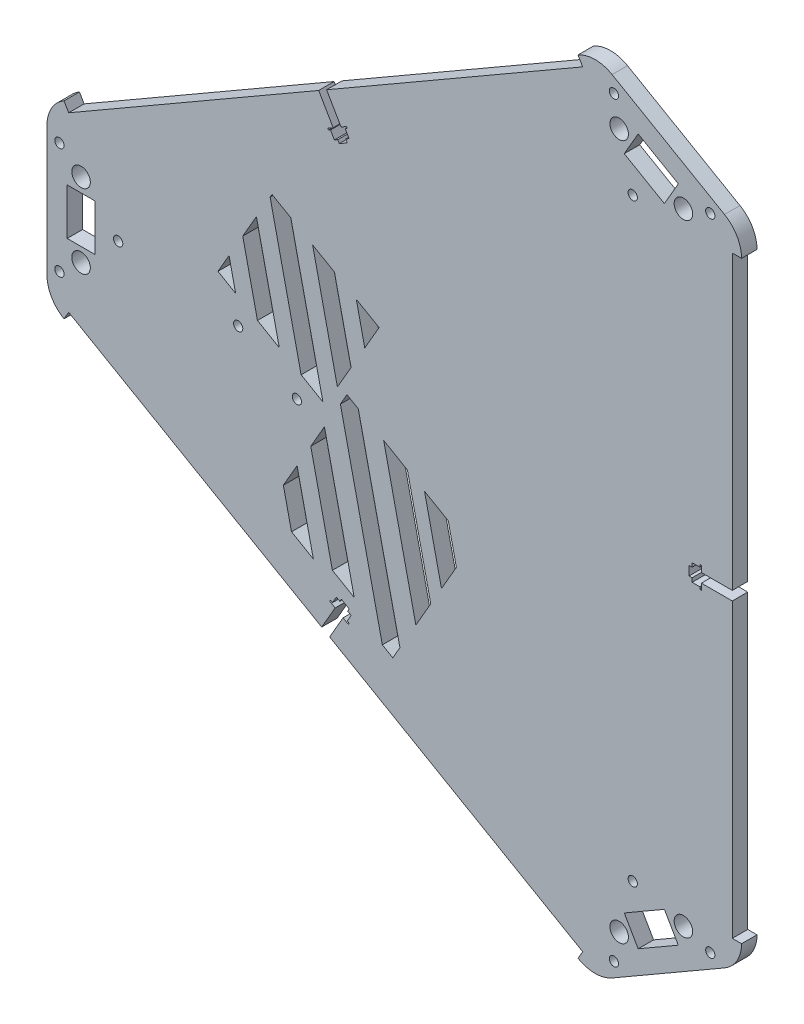
SolidWorks part; units mm, degrees
material "6061-T6 Black anodised"
ref_plane "Front Plane" through (0, 0, 0) normal (0, 0, 1) x (1, 0, 0)
ref_plane "Top Plane" through (0, 0, 0) normal (0, 1, 0) x (1, 0, 0)
ref_plane "Right Plane" through (0, 0, 0) normal (1, 0, 0) x (0, 0, -1)
sketch "Sketch1" plane through (0, 0, 0) normal (0, 0, 1) x (1, 0, 0)
  line L0 (0, 0) -> (-123, 0) construction
  line L1 (-123, 21) -> (-123, -21) construction
  line L2 (-131.025, 20.9813) -> (-131.025, -21) construction
  line L3 (0, 0) -> (61.5, 106.5211) construction
  line L4 (0, 0) -> (61.5, -106.5211) construction
  line L5 (43.3135, 117.0211) -> (79.6865, 96.0211) construction
  line L6 (79.6865, -96.0211) -> (43.3135, -117.0211) construction
  line L7 (47.326, 123.971) -> (83.699, 102.971) construction
  line L8 (83.699, -102.971) -> (47.326, -123.971) construction
  line L9 (-127.0125, 27.9499) -> (39.301, 123.971)
  line L10 (87.7115, 96.0211) -> (87.7115, -96.0211)
  line L11 (39.301, -123.971) -> (-127.0125, -27.9498)
  line L12 (57.2548, -114.1682) -> (70.2452, -106.6682)
  line L13 (57.2548, -114.1682) -> (52.7548, -106.374)
  line L14 (70.2452, -106.6682) -> (65.7452, -98.874)
  line L15 (52.7548, -106.374) -> (65.7452, -98.874)
  line L16 (57.2548, -114.1682) -> (65.7452, -98.874) construction
  line L17 (70.2452, -106.6682) -> (52.7548, -106.374) construction
  line L18 (-118.5, 7.5) -> (-118.5, -7.5)
  line L19 (-127.5, -7.5) -> (-118.5, -7.5)
  line L20 (-127.5, 7.5) -> (-127.5, -7.5)
  line L21 (-127.5, 7.5) -> (-118.5, 7.5)
  line L22 (65.7452, 98.874) -> (52.7548, 106.374)
  line L23 (57.2548, 114.1682) -> (52.7548, 106.374)
  line L24 (70.2452, 106.6682) -> (57.2548, 114.1682)
  line L25 (70.2452, 106.6682) -> (65.7452, 98.874)
  line L26 (-123, 21) -> (-99, 34.8564) construction
  line L27 (-99, 34.8564) -> (-99, -34.8564) construction
  line L28 (-99, -34.8564) -> (-123, -21) construction
  line L29 (-134.025, 21) -> (-134.025, -21)
  line L30 (-127.0125, 27.9499) -> (-128.5125, 30.5479)
  line L31 (-127.0125, -27.9498) -> (-128.5125, -30.5479)
  line L32 (39.301, 123.971) -> (37.801, 126.5691)
  line L33 (87.7115, 96.0211) -> (90.7115, 96.0211)
  line L34 (48.826, 126.5691) -> (85.199, 105.5691)
  line L35 (39.301, -123.971) -> (37.801, -126.5691)
  line L36 (87.7115, -96.0211) -> (90.7115, -96.0211)
  line L37 (48.826, -126.5691) -> (85.199, -105.5691)
  circle A0 centre (-123, 21) radius 4.025 construction
  circle A1 centre (-123, -21) radius 4.025 construction
  arc A2 (-127.0125, 27.9499) -> (-131.025, 20.9813) centre (-123, 21) ccw construction
  arc A3 (-131.025, -21) -> (-127.0125, -27.9498) centre (-123, -21) ccw construction
  circle A4 centre (43.3135, 117.0211) radius 4.025 construction
  circle A5 centre (79.6865, 96.0211) radius 4.025 construction
  circle A6 centre (79.6865, -96.0211) radius 4.025 construction
  circle A7 centre (43.3135, -117.0211) radius 4.025 construction
  arc A8 (39.301, -123.971) -> (47.326, -123.971) centre (43.3135, -117.0211) ccw construction
  arc A9 (83.699, -102.971) -> (87.7115, -96.0211) centre (79.6865, -96.0211) ccw construction
  arc A10 (87.7115, 96.0211) -> (83.699, 102.971) centre (79.6865, 96.0211) ccw construction
  arc A11 (47.326, 123.971) -> (39.301, 123.971) centre (43.3135, 117.0211) ccw construction
  circle A12 centre (-99, 34.8564) radius 1.65 construction
  circle A13 centre (-99, -34.8564) radius 1.65 construction
  circle A14 centre (79.6865, 68.3083) radius 1.65 construction
  circle A15 centre (19.3135, 103.1647) radius 1.65 construction
  circle A16 centre (19.3135, -103.1647) radius 1.65 construction
  circle A17 centre (79.6865, -68.3083) radius 1.65 construction
  circle A18 centre (0, 0) radius 65 construction
  arc A19 (-134.025, 21) -> (-128.5125, 30.5479) centre (-123, 21) cw
  arc A20 (-134.025, -21) -> (-128.5125, -30.5479) centre (-123, -21) ccw
  arc A21 (48.826, 126.5691) -> (37.801, 126.5691) centre (43.3135, 117.0211) ccw
  arc A22 (90.7115, 96.0211) -> (85.199, 105.5691) centre (79.6865, 96.0211) ccw
  arc A23 (37.801, -126.5691) -> (48.826, -126.5691) centre (43.3135, -117.0211) ccw
  arc A24 (85.199, -105.5691) -> (90.7115, -96.0211) centre (79.6865, -96.0211) ccw
  circle A25 centre (-123, 12) radius 3
  circle A26 centre (-123, -12) radius 3
  circle A27 centre (71.8923, 100.5211) radius 3
  circle A28 centre (51.1077, 112.5211) radius 3
  circle A29 centre (51.1077, -112.5211) radius 3
  circle A30 centre (71.8923, -100.5211) radius 3
  circle A31 centre (-111, 0) radius 1.5
  circle A32 centre (55.5, 96.1288) radius 1.5
  circle A33 centre (55.5, -96.1288) radius 1.5
  circle A34 centre (-130, 18) radius 1.5
  circle A35 centre (-130, -18) radius 1.5
  circle A36 centre (80.5885, 103.5833) radius 1.5
  circle A37 centre (49.4115, 121.5833) radius 1.5
  circle A38 centre (49.4115, -121.5833) radius 1.5
  circle A39 centre (80.5885, -103.5833) radius 1.5
  point P44 (0, 0)
  point P56 (0, 0)
  point P79 (0, 0)
  point P84 (0, 0)
  point P91 (0, 0)
  point P104 (0, 0)
  dimension "D3" = 8.05
  dimension "D9" = 3.3
  dimension "D12" = 130
  dimension "D15" = 6
  dimension "D18" = 3
  dimension "D24" = 3
  dimension "D1" = 123
  dimension "D2" = 42
  dimension "D4" = 120
  dimension "D5" = 4
  dimension "D6" = 9
  dimension "D7" = 15
  dimension "D10" = 24
  dimension "D13" = 3
  dimension "D14" = 12
  dimension "D16" = 12
  dimension "D19" = 12
  dimension "D21" = 3
  dimension "D22" = 7
  dimension "D8" = 3
  dimension "D11" = 3
  dimension "D17" = 3
  dimension "D20" = 3
  dimension "D23" = 3
extrude "Boss-Extrude1" add sketch "Sketch1" along normal blind 5
sketch "Sketch2" plane through (0, 0, 5) normal (0, 0, 1) x (1, 0, 0)
  line L0 (0, 0) -> (87.7115, 0) construction
  line L1 (87.7115, -96.0211) -> (87.7115, 96.0211) construction
  line L2 (87.7115, 1.48) -> (77.7115, 1.48)
  line L3 (77.7115, 1.48) -> (77.7115, 3.5)
  line L4 (77.7115, 3.5) -> (77.2115, 3.5)
  line L5 (77.2115, 3.5) -> (77.2115, 2.75)
  line L6 (77.2115, 2.75) -> (74.7115, 2.75)
  line L7 (74.7115, 2.75) -> (74.7115, 1.48)
  line L8 (74.7115, 1.48) -> (73.7115, 1.48)
  line L9 (73.7115, 1.48) -> (73.7115, -1.48)
  line L10 (87.7115, -1.48) -> (87.7115, 1.48)
  line L11 (74.7115, -1.48) -> (73.7115, -1.48)
  line L12 (74.7115, -2.75) -> (74.7115, -1.48)
  line L13 (77.2115, -2.75) -> (74.7115, -2.75)
  line L14 (77.2115, -3.5) -> (77.2115, -2.75)
  line L15 (77.7115, -3.5) -> (77.2115, -3.5)
  line L16 (77.7115, -1.48) -> (77.7115, -3.5)
  line L17 (87.7115, -1.48) -> (77.7115, -1.48)
  line L18 (-43.2236, -77.8254) -> (-38.2236, -69.1652)
  line L19 (-38.2236, -69.1652) -> (-36.4742, -70.1752)
  line L20 (-36.4742, -70.1752) -> (-36.2242, -69.7421)
  line L21 (-36.2242, -69.7421) -> (-36.8737, -69.3671)
  line L22 (-36.8737, -69.3671) -> (-35.6237, -67.2021)
  line L23 (-35.6237, -67.2021) -> (-36.7236, -66.5671)
  line L24 (-36.7236, -66.5671) -> (-36.2236, -65.7011)
  line L25 (-36.2236, -65.7011) -> (-38.787, -64.2211)
  line L26 (-39.287, -65.0871) -> (-38.787, -64.2211)
  line L27 (-40.3869, -64.4521) -> (-39.287, -65.0871)
  line L28 (-41.6369, -66.6171) -> (-40.3869, -64.4521)
  line L29 (-42.2864, -66.2421) -> (-41.6369, -66.6171)
  line L30 (-42.5364, -66.6752) -> (-42.2864, -66.2421)
  line L31 (-40.787, -67.6852) -> (-42.5364, -66.6752)
  line L32 (-45.787, -76.3454) -> (-40.787, -67.6852)
  line L33 (-45.787, -76.3454) -> (-43.2236, -77.8254)
  line L34 (-46.4365, 75.2204) -> (-41.4365, 66.5602)
  line L35 (-41.4365, 66.5602) -> (-43.1859, 65.5502)
  line L36 (-43.1859, 65.5502) -> (-42.9359, 65.1171)
  line L37 (-42.9359, 65.1171) -> (-42.2864, 65.4921)
  line L38 (-42.2864, 65.4921) -> (-41.0364, 63.3271)
  line L39 (-41.0364, 63.3271) -> (-39.9365, 63.9621)
  line L40 (-39.9365, 63.9621) -> (-39.4365, 63.0961)
  line L41 (-39.4365, 63.0961) -> (-36.8731, 64.5761)
  line L42 (-37.3731, 65.4421) -> (-36.8731, 64.5761)
  line L43 (-36.2732, 66.0771) -> (-37.3731, 65.4421)
  line L44 (-37.5232, 68.2421) -> (-36.2732, 66.0771)
  line L45 (-36.8737, 68.6171) -> (-37.5232, 68.2421)
  line L46 (-37.1237, 69.0502) -> (-36.8737, 68.6171)
  line L47 (-38.8731, 68.0402) -> (-37.1237, 69.0502)
  line L48 (-43.8731, 76.7004) -> (-38.8731, 68.0402)
  line L49 (-43.8731, 76.7004) -> (-46.4365, 75.2204)
  point P16 (73.7115, 0)
  point P56 (0.0125, 0.0072)
  point P58 (-0.6495, -0.375)
  point P59 (0, 0)
  dimension "D1" = 0.5
  dimension "D2" = 2.5
  dimension "D3" = 14
  dimension "D4" = 2.96
  dimension "D5" = 7
  dimension "D6" = 5.5
  dimension "D7" = 1
  dimension "D8" = 3
extrude "Cut-Extrude1" cut sketch "Sketch2" against normal through all
sketch "Sketch3" plane through (0, 0, 5) normal (0, 0, 1) x (1, 0, 0)
  line L0 (-36.9705, -6.0348) -> (-61.9705, -49.336) construction
  line L1 (-36.9705, -6.0348) -> (2.8667, -29.0348) construction
  line L2 (-61.9705, -49.336) -> (-22.1333, -72.3361) construction
  line L3 (2.8667, -29.0348) -> (-22.1333, -72.3361) construction
  line L4 (-36.9705, -6.0348) -> (-22.1333, -72.3361) construction
  line L5 (-61.9705, -49.336) -> (2.8667, -29.0348) construction
  line L6 (-36.8558, -63.8361) -> (-43.8558, -75.9604) construction
  line L7 (-42.574, -76.7004) -> (39.301, -123.971) construction
  line L8 (-57.5395, -41.6614) -> (-54.9098, -53.4125)
  line L9 (-54.9098, -53.4125) -> (-47.8492, -57.489)
  line L10 (-47.8492, -57.489) -> (-53.1086, -33.9868)
  line L11 (-53.1086, -33.9868) -> (-57.5395, -41.6614)
  line L12 (-48.6777, -26.3122) -> (-41.6788, -57.5874)
  line L13 (-35.5924, -64.5655) -> (-28.5317, -68.6419) construction
  line L14 (-34.6181, -61.6639) -> (-44.2467, -18.6376)
  line L15 (-44.2467, -18.6376) -> (-48.6777, -26.3122)
  line L16 (-39.0937, -9.7122) -> (-25.5166, -70.3827)
  line L17 (-25.5166, -70.3827) -> (-22.1333, -72.3361)
  line L18 (-22.1333, -72.3361) -> (-19.8255, -68.3389)
  line L19 (-19.8255, -68.3389) -> (-33.2931, -8.1579)
  line L20 (-44.2467, -18.6376) -> (-37.4373, -17.1137) construction
  line L21 (-25.0817, -12.8988) -> (-14.6725, -59.4135)
  line L22 (-14.6725, -59.4135) -> (-9.8562, -51.0715)
  line L23 (-9.8562, -51.0715) -> (-17.4071, -17.3297)
  line L24 (-17.4071, -17.3297) -> (-25.0817, -12.8988)
  line L25 (-11.8686, -20.5274) -> (-6.3805, -45.0514)
  line L26 (-6.3805, -45.0514) -> (-1.5643, -36.7094)
  line L27 (-1.5643, -36.7094) -> (-4.194, -24.9583)
  line L28 (-4.194, -24.9583) -> (-11.8686, -20.5274)
  line L29 (-33.2931, -8.1579) -> (-36.9705, -6.0348)
  line L30 (-36.9705, -6.0348) -> (-39.0937, -9.7122)
  line L31 (-25.0817, -12.8988) -> (-31.8911, -14.4226) construction
  line L32 (-45.1375, -75.2204) -> (-42.574, -76.7004) construction
  line L33 (-41.6788, -57.5874) -> (-34.6181, -61.6639)
  point P1 (-29.5519, -39.1854)
  dimension "D1" = 3
  dimension "D2" = 46
  dimension "D3" = 50
  dimension "D4" = 14
  dimension "D5" = 6
  dimension "D6" = 6
  dimension "D7" = 6
  dimension "D8" = 6
  dimension "D9" = 6
  dimension "D10" = 17
extrude "Cut-Extrude2" cut sketch "Sketch3" against normal through all
sketch "Sketch4" plane through (0, 0, 5) normal (0, 0, 1) x (1, 0, 0)
  line L0 (-127.0125, -27.9498) -> (-45.1375, -75.2204) construction
  line L1 (-128.5125, -30.5479) -> (-127.0125, -27.9498) construction
  circle A0 centre (-72.1758, -4.3808) radius 1.5
  circle A1 centre (-53.1624, -15.3581) radius 1.5
  dimension "D3" = 3
  dimension "D6" = 3
  dimension "D1" = 47.8298
  dimension "D2" = 35.7054
  dimension "D4" = 21.9547
  dimension "D5" = 47.8298
sketch "Sketch5" plane through (0, 0, 5) normal (0, 0, 1) x (1, 0, 0)
  line L0 (-71.5686, -59.9604) -> (-26.5686, 17.9819) construction
  line L1 (-127.0125, -27.9498) -> (-45.1375, -75.2204) construction
  line L2 (-26.5686, 17.9819) -> (-61.2096, 37.9819) construction
  line L3 (-61.2096, 37.9819) -> (-78.7096, 7.671) construction
  line L4 (-78.7096, 7.671) -> (-44.0686, -12.329) construction
  line L5 (-36.9705, -6.0348) -> (-39.0937, -9.7122) construction
  line L6 (-40.0613, -5.3882) -> (-48.069, 30.3952)
  line L7 (-48.069, 30.3952) -> (-41.0084, 26.3187)
  line L8 (-41.0084, 26.3187) -> (-35.6303, 2.2864)
  line L9 (-35.6303, 2.2864) -> (-40.0613, -5.3882)
  line L10 (-39.0937, -9.7122) -> (-25.5166, -70.3827) construction
  line L11 (-66.256, 29.2412) -> (-58.865, -3.7863)
  line L12 (-33.9477, 22.2422) -> (-31.1994, 9.961)
  line L13 (-31.1994, 9.961) -> (-26.5686, 17.9819)
  line L14 (-26.5686, 17.9819) -> (-33.9477, 22.2422)
  line L15 (-55.1297, 34.4717) -> (-44.7437, -11.9392)
  line L16 (-44.7437, -11.9392) -> (-51.8043, -7.8628)
  line L17 (-51.8043, -7.8628) -> (-61.8251, 36.9158)
  line L18 (-61.8251, 36.9158) -> (-61.2096, 37.9819)
  line L19 (-61.2096, 37.9819) -> (-55.1297, 34.4717)
  line L20 (-58.865, -3.7863) -> (-65.9256, 0.2902)
  line L21 (-65.9256, 0.2902) -> (-70.687, 21.5666)
  line L22 (-70.687, 21.5666) -> (-66.256, 29.2412)
  line L23 (-75.1179, 13.892) -> (-72.9863, 4.3666)
  line L24 (-72.9863, 4.3666) -> (-78.7096, 7.671)
  line L26 (-78.7096, 7.671) -> (-75.1179, 13.892)
  dimension "D1" = 3
  dimension "D2" = 6
  dimension "D3" = 6
  dimension "D4" = 35
  dimension "D5" = 55
  dimension "D6" = 40
  dimension "D7" = 6
  dimension "D8" = 6
  dimension "D9" = 6
  dimension "D10" = 6
  dimension "D11" = 6
extrude "Cut-Extrude3" cut sketch "Sketch5" against normal blind 10
extrude "Cut-Extrude4" cut sketch "Sketch4" against normal blind 10
equation "\"D16@Sketch1\"=\"D14@Sketch1\""
